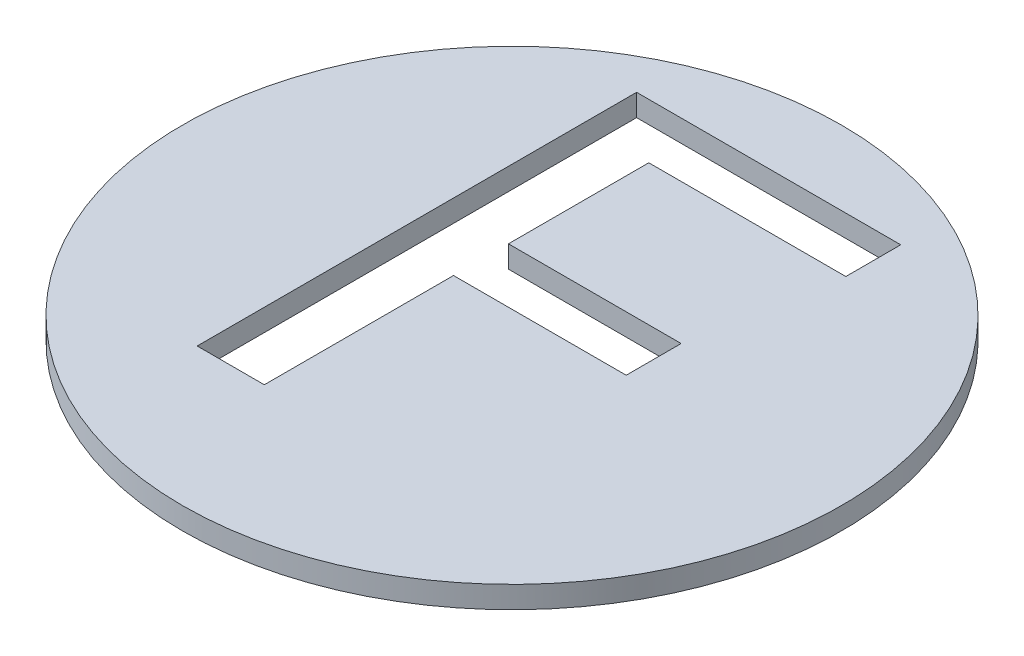
SolidWorks part; units mm, degrees
ref_plane "Front Plane" through (0, 0, 0) normal (0, 0, 1) x (1, 0, 0)
ref_plane "Top Plane" through (0, 0, 0) normal (0, 1, 0) x (1, 0, 0)
ref_plane "Right Plane" through (0, 0, 0) normal (1, 0, 0) x (0, 0, -1)
sketch "Sketch1" plane through (0, 0, 0) normal (0, 1, 0) x (1, 0, 0)
  circle A0 centre (0, 0) radius 45
  text T0 "F" font "3ds" height 60
  point P4 (-20.6592, -23.8179)
  point P5 (-16.0493, -19.5494)
  dimension "D1" = 90
extrude "Boss-Extrude1" add sketch "Sketch1" along normal blind 3
